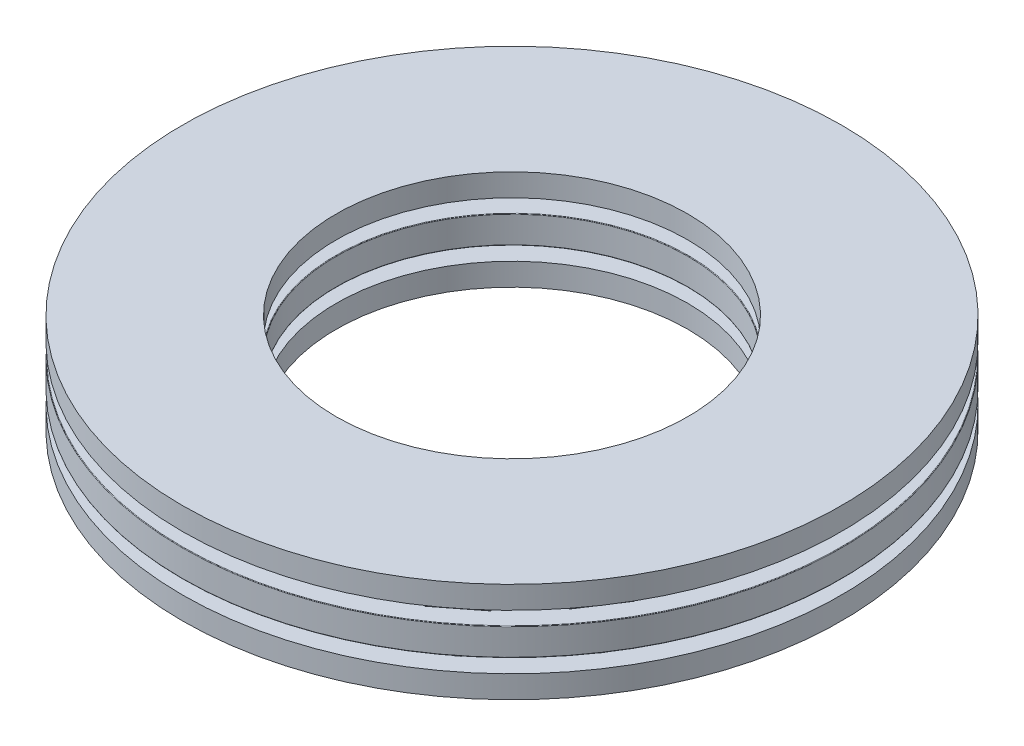
SolidWorks part; units mm, degrees
ref_plane "Front Plane" through (0, 0, 0) normal (0, 0, 1) x (1, 0, 0)
ref_plane "Top Plane" through (0, 0, 0) normal (0, 1, 0) x (1, 0, 0)
ref_plane "Right Plane" through (0, 0, 0) normal (1, 0, 0) x (0, 0, -1)
sketch "Sketch1" plane through (0, 0, 0) normal (1, 0, 0) x (0, 0, -1)
  line L0 (-11.9062, 0) -> (11.9062, 0) construction
  line L1 (0, -0.9922) -> (0, 0.9922) construction
  line L2 (-11.9063, 0.4961) -> (-6.35, 0.4961)
  line L3 (-11.9063, 0.4961) -> (-11.9063, -0.4961)
  line L4 (-11.9063, -0.4961) -> (-6.35, -0.4961)
  line L5 (-6.35, 0.4961) -> (-6.35, -0.4961)
  line L7 (-9.1281, 0.9922) -> (-9.1281, 0.4961) construction
  line L8 (-11.2117, 0.9922) -> (-7.0445, 0.9922) construction
  line L9 (-11.2117, 0.9922) -> (-11.2117, -0.9922) construction
  line L10 (-11.2117, -0.9922) -> (-7.0445, -0.9922) construction
  line L11 (-7.0445, 0.9922) -> (-7.0445, -0.9922) construction
  point P16 (-11.2117, 0)
  dimension "D1" = 4.1672
  dimension "OD" = 23.8125
  dimension "Shaft Dia" = 12.7
  dimension "Th" = 1.9844
  dimension "D2" = 0.9922
  dimension "D3" = 5.5562
revolve "Revolve1" add sketch "Sketch1" angle 360 about L1
sketch "Sketch3" plane through (0, 0, 0) normal (1, 0, 0) x (0, 0, -1)
  line L0 (-11.2117, 0.9922) -> (-11.2117, -0.9922) construction
  line L1 (-11.2117, 0) -> (-7.0445, 0)
  line L2 (-11.2117, 0) -> (-11.2117, 0.9922)
  line L3 (-11.2117, 0.9922) -> (-7.0445, 0.9922)
  line L4 (-7.0445, 0) -> (-7.0445, 0.9922)
revolve "Cut-Revolve1" cut sketch "Sketch3" angle 360 about L1
sketch "Sketch2" plane through (0, 0, 0) normal (1, 0, 0) x (0, 0, -1)
  line L1 (-11.2117, 0) -> (-7.0445, 0)
  line L2 (-11.2117, 0) -> (-11.2117, 0.9922)
  line L3 (-11.2117, 0.9922) -> (-7.0445, 0.9922)
  line L4 (-7.0445, 0) -> (-7.0445, 0.9922)
revolve "Revolve2" add sketch "Sketch2" angle 360 about L1
ref_axis "Axis1" through (0, 0.9922, 0) along (0, -1, 0)
pattern_circular "CirPattern1" count 19 every 18.947 about axis through (0, 0.9922, 0) along (0, -1, 0) of bodies 187 411
pattern_circular "CirPattern2" count 19 every 18.947 about axis through (0, 0, 0) along (0, 1, 0) of "Cut-Revolve1"
sketch "Sketch4" plane through (0, 0, 0) normal (1, 0, 0) x (0, 0, -1)
  line L0 (-11.9063, 0.4961) -> (-11.9063, -0.4961) construction
  line L1 (-11.9062, 0.9922) -> (-6.35, 0.9922)
  line L2 (-11.9062, 0.9922) -> (-11.9062, 1.805)
  line L3 (-11.9062, 1.805) -> (-6.35, 1.805)
  line L4 (-6.35, 0.9922) -> (-6.35, 1.805)
  line L5 (-11.9062, -1.805) -> (-6.35, -1.805)
  line L6 (-11.9062, -1.805) -> (-11.9062, -0.9922)
  line L7 (-11.9062, -0.9922) -> (-6.35, -0.9922)
  line L8 (-6.35, -1.805) -> (-6.35, -0.9922)
  line L10 (-6.35, 0.4961) -> (-6.35, -0.4961) construction
  line L11 (0, 0) -> (-11.9062, 0) construction
  line L12 (-11.9062, 0) -> (11.9062, 0) construction
  line L13 (0, -0.9922) -> (0, 0.9922) construction
  dimension "Ht" = 3.61
  dimension "Washer Th" = 0.8128
  dimension "Washer ID" = 12.7
  dimension "Washer OD" = 23.8125
revolve "Revolve3" add sketch "Sketch4" angle 360 about L1
fillet "Fillet1" [suppressed] radius 0.0198
fillet "Fillet2" radius 0.0198 4 edges at (0, -0.4961, -6.35) (0, 0.4961, -6.35) (0, -0.4961, -11.9063) (0, 0.4961, -11.9063)
fillet "Fillet3" [suppressed] radius 0.0198
equation "\"D2@Sketch1\" = \"Th@Sketch1\"*.5"
equation "\"D1@Fillet1\" = \"Th@Sketch1\"*.01"
equation "\"D1@Fillet2\" = \"D1@Fillet1\""
equation "\"D1@Fillet3\" = \"D1@Fillet1\""
equation "\"D1@Sketch1\" = \"D3@Sketch1\"*.75"
equation "\"Angle@CirPattern1\" = 360/\"Rollers@CirPattern1\""
equation "\"Rollers@CirPattern1\" = \"OD@Sketch1\"*20"
equation "\"D1@CirPattern2\" = \"Rollers@CirPattern1\""
equation "\"D2@CirPattern2\" = \"Angle@CirPattern1\""
equation "\"Ht@Sketch4\"=\"Th@Sketch1\"+0.09-0.0130in -0.0130in "
